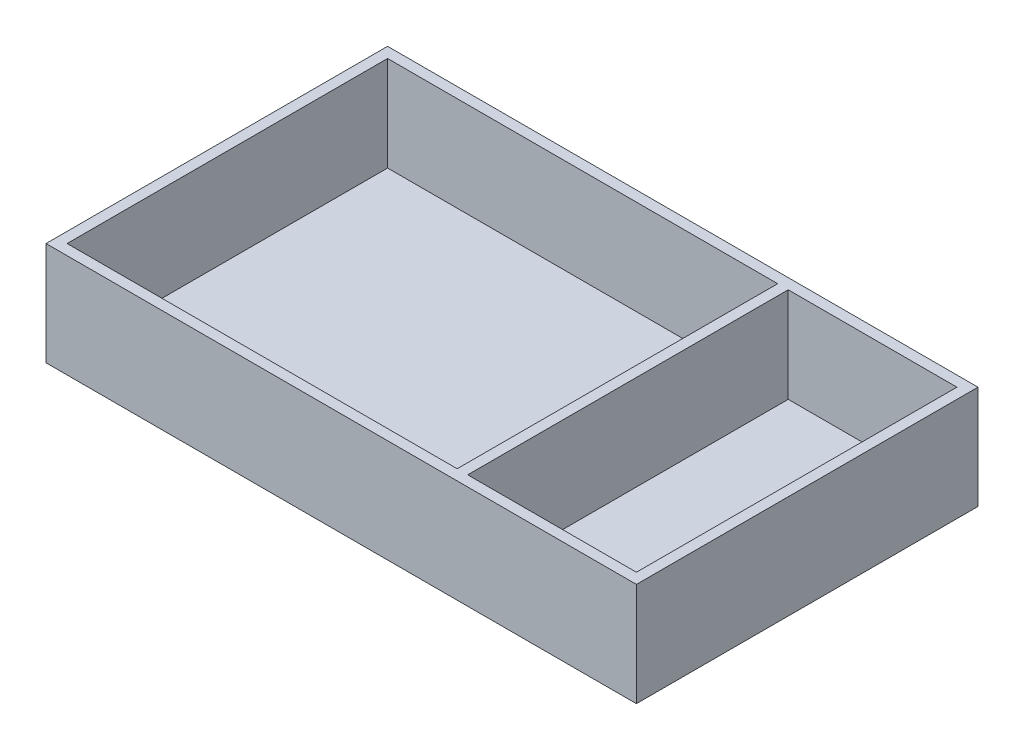
SolidWorks part; units mm, degrees
ref_plane "Alzado" through (0, 0, 0) normal (0, 0, 1) x (1, 0, 0)
ref_plane "Planta" through (0, 0, 0) normal (0, 1, 0) x (1, 0, 0)
ref_plane "Vista lateral" through (0, 0, 0) normal (1, 0, 0) x (0, 0, -1)
sketch "Croquis1" plane through (0, 0, 0) normal (0, 1, 0) x (1, 0, 0)
  line L1 (-135, -76) -> (135, -76)
  line L2 (-135, -76) -> (-135, 76)
  line L3 (-135, 76) -> (135, 76)
  line L4 (135, -76) -> (135, 76)
  line L5 (-135, -76) -> (135, 76) construction
  line L6 (-135, 76) -> (135, -76) construction
  line L7 (-140, -81) -> (140, -81)
  line L8 (-140, -81) -> (-140, 81)
  line L9 (-140, 81) -> (140, 81)
  line L10 (140, -81) -> (140, 81)
  line L11 (-140, -81) -> (140, 81) construction
  line L12 (-140, 81) -> (140, -81) construction
  point P0 (0, 0)
  point P5 (0, 0)
  dimension "D1" = 152
  dimension "D2" = 270
  dimension "D3" = 5
  dimension "D4" = 5
extrude "Saliente-Extruir1" add sketch "Croquis1" along normal blind 45
sketch "Croquis3" plane through (0, 0, 0) normal (0, -1, 0) x (1, 0, 0)
  line L1 (-140, 81) -> (140, 81)
  line L2 (-140, 81) -> (-140, -81)
  line L3 (-140, -81) -> (140, -81)
  line L4 (140, 81) -> (140, -81)
extrude "Saliente-Extruir2" add sketch "Croquis3" along normal blind 4
sketch "Croquis4" plane through (0, 0, 0) normal (0, 1, 0) x (1, 0, 0)
  line L0 (135, 76) -> (-135, 76) construction
  line L1 (55, 76) -> (50, 76)
  line L2 (55, 76) -> (55, -76)
  line L3 (55, -76) -> (50, -76)
  line L4 (50, 76) -> (50, -76)
  line L5 (-135, -76) -> (135, -76) construction
  line L6 (135, -76) -> (135, 76) construction
  dimension "D1" = 5
  dimension "D2" = 80
extrude "Saliente-Extruir3" add sketch "Croquis4" along normal blind 45
